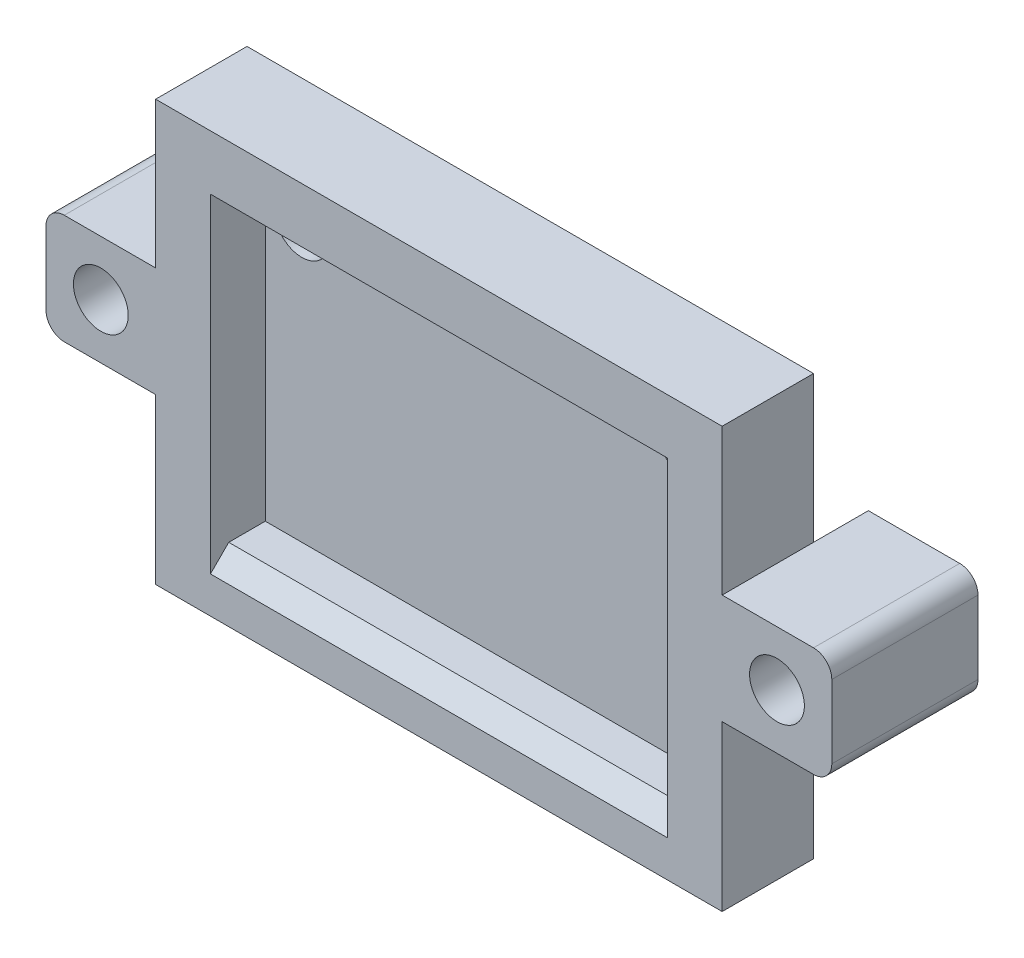
SolidWorks part; units mm, degrees
ref_plane "Plan de face" through (0, 0, 0) normal (0, 0, 1) x (1, 0, 0)
ref_plane "Plan de dessus" through (0, 0, 0) normal (0, 1, 0) x (1, 0, 0)
ref_plane "Plan de droite" through (0, 0, 0) normal (1, 0, 0) x (0, 0, -1)
sketch "Esquisse1" plane through (0, 0, 0) normal (0, 0, 1) x (1, 0, 0)
  line L1 (-31, 23) -> (0, 23)
  line L2 (-31, 23) -> (-31, 0)
  line L3 (-31, 0) -> (0, 0)
  line L4 (0, 23) -> (0, 0)
  dimension "D1" = 31
  dimension "D2" = 23
extrude "Boss.-Extru.1" add sketch "Esquisse1" along normal blind 5
sketch "Esquisse2" plane through (0, 0, 5) normal (0, 0, 1) x (1, 0, 0)
  line L0 (-31, 23) -> (-31, 0) construction
  line L1 (-28, 20) -> (-3, 20)
  line L2 (-28, 20) -> (-28, 3)
  line L3 (-28, 3) -> (-3, 3)
  line L4 (-3, 20) -> (-3, 3)
  line L5 (0, 23) -> (-31, 23) construction
  dimension "D1" = 25
  dimension "D2" = 17
  dimension "D3" = 3
  dimension "D4" = 3
extrude "Enlèv. mat.-Extru.1" cut sketch "Esquisse2" against normal blind 3
sketch "Esquisse3" plane through (0, 0, 2) normal (0, 0, 1) x (1, 0, 0)
  line L0 (-3, 3) -> (-3, 20) construction
  line L1 (-3, 20) -> (-28, 20) construction
  line L2 (-28, 20) -> (-28, 3) construction
  line L3 (-3, 20) -> (-28, 20) construction
  circle A0 centre (-26, 18) radius 1.5
  circle A1 centre (-5, 18) radius 1.5
  dimension "D1" = 3
  dimension "D2" = 3
  dimension "D3" = 2
  dimension "D4" = 2
  dimension "D5" = 2
  dimension "D6" = 2
sketch "Esquisse4" plane through (0, 0, 5) normal (0, 0, 1) x (1, 0, 0)
  line L0 (-28, 3) -> (-3, 3) construction
  line L1 (-31, 15) -> (-37, 15)
  line L2 (-31, 15) -> (-31, 9)
  line L3 (-31, 9) -> (-37, 9)
  line L4 (-37, 15) -> (-37, 9)
  line L5 (6, 15) -> (0, 15)
  line L6 (6, 15) -> (6, 9)
  line L7 (6, 9) -> (0, 9)
  line L8 (0, 15) -> (0, 9)
  line L11 (-31, 23) -> (-31, 0) construction
  line L12 (0, 0) -> (0, 23) construction
  dimension "D1" = 6
  dimension "D2" = 6
  dimension "D3" = 6
  dimension "D4" = 6
  dimension "D5" = 6
  dimension "D6" = 6
extrude "Boss.-Extru.3" add sketch "Esquisse4" against normal blind 8
chamfer "Chanfrein2" distance 1 angle 45 1 edges at (-15.5, 3, 5)
fillet "Congé2" radius 1 4 edges at (-37, 15, 1) (6, 15, 1) (6, 9, 1) (-37, 9, 1)
extrude "Enlèv. mat.-Extru.2" cut sketch "Esquisse3" against normal blind 3
sketch "Esquisse5" plane through (0, 0, 5) normal (0, 0, 1) x (1, 0, 0)
  line L0 (0, 9) -> (5, 9) construction
  line L1 (6, 10) -> (6, 14) construction
  line L2 (-36, 9) -> (-31, 9) construction
  line L3 (-37, 14) -> (-37, 10) construction
  circle A0 centre (-34, 12) radius 1.5
  circle A1 centre (3, 12) radius 1.5
  dimension "D1" = 3
  dimension "D2" = 3
  dimension "D3" = 3
  dimension "D4" = 3
  dimension "D5" = 3
  dimension "D6" = 3
extrude "Enlèv. mat.-Extru.3" cut sketch "Esquisse5" against normal through all
